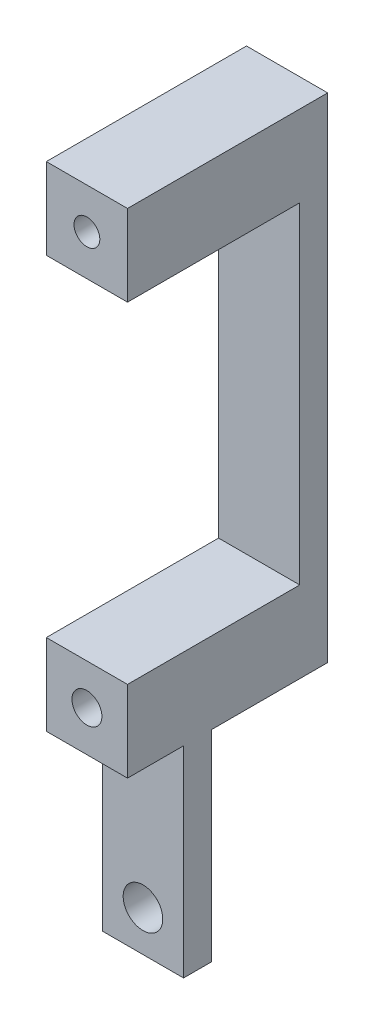
SolidWorks part; units mm, degrees
ref_plane "Front Plane" through (0, 0, 0) normal (0, 0, 1) x (1, 0, 0)
ref_plane "Top Plane" through (0, 0, 0) normal (0, 1, 0) x (1, 0, 0)
ref_plane "Right Plane" through (0, 0, 0) normal (1, 0, 0) x (0, 0, -1)
sketch "Sketch1" plane through (0, 0, 0) normal (0, 0, 1) x (1, 0, 0)
  line L1 (0, 0) -> (13.843, 0)
  line L2 (0, 0) -> (0, 48.133)
  line L3 (0, 48.133) -> (13.843, 48.133)
  line L4 (13.843, 0) -> (13.843, 48.133)
  dimension "D1" = 48.133
  dimension "D2" = 13.843
extrude "Boss-Extrude1" add sketch "Sketch1" along normal blind 4.7625
sketch "Sketch2" plane through (0, 0, 4.7625) normal (0, 0, 1) x (1, 0, 0)
  line L0 (13.843, 0) -> (13.843, 48.133) construction
  line L1 (0, 48.133) -> (13.843, 48.133)
  line L2 (0, 48.133) -> (0, 34.29)
  line L3 (0, 34.29) -> (13.843, 34.29)
  line L4 (13.843, 48.133) -> (13.843, 34.29)
  dimension "D1" = 13.843
extrude "Boss-Extrude2" add sketch "Sketch2" along normal blind 9.5567
sketch "Sketch3" plane through (0, 0, 0) normal (0, 0, -1) x (-1, 0, 0)
  line L0 (0, 0) -> (-13.843, 0) construction
  circle A0 centre (-6.9215, 6.9215) radius 3.3782
  point P2 (0, 0)
  point P5 (-6.9215, 0)
  dimension "D1" = 6.9215
  dimension "D2" = 6.7564
extrude "Cut-Extrude1" cut sketch "Sketch3" against normal blind 9.5567
sketch "Sketch4" plane through (0, 0, 0) normal (0, 0, -1) x (-1, 0, 0)
  line L0 (-13.843, 48.133) -> (0, 48.133) construction
  circle A0 centre (-6.9215, 41.2115) radius 2.5527
  point P1 (0, 0)
  point P5 (-6.9215, 48.133)
  dimension "D2" = 5.1054
  dimension "D1" = 6.9215
extrude "Cut-Extrude2" cut sketch "Sketch4" against normal blind 16.9228
sketch "Sketch5" plane through (0, 0, 0) normal (0, 0, -1) x (-1, 0, 0)
  line L0 (0, 48.133) -> (0, 0) construction
  line L1 (-13.843, 48.133) -> (0, 48.133)
  line L2 (-13.843, 48.133) -> (-13.843, 34.29)
  line L3 (-13.843, 34.29) -> (0, 34.29)
  line L4 (0, 48.133) -> (0, 34.29)
  dimension "D1" = 13.843
extrude "Boss-Extrude3" add sketch "Sketch5" along normal blind 19.812
sketch "Sketch6" plane through (0, 0, -19.812) normal (0, 0, -1) x (-1, 0, 0)
  line L0 (0, 34.29) -> (0, 48.133) construction
  line L1 (-9.7319, 46.0829) -> (-12.5454, 41.2133)
  line L2 (-12.5454, 41.2133) -> (-9.735, 36.342)
  line L3 (-9.735, 36.342) -> (-4.1111, 36.3401)
  line L4 (-4.1111, 36.3401) -> (-1.2976, 41.2097)
  line L5 (-1.2976, 41.2097) -> (-4.108, 46.081)
  line L6 (-4.108, 46.081) -> (-9.7319, 46.0829)
  line L7 (0, 48.133) -> (-13.843, 48.133) construction
  circle A0 centre (-6.9215, 41.2115) radius 4.8704 construction
  point P1 (0, 0)
  point P11 (0, 41.2115)
  point P12 (0, 0)
  point P15 (-6.9215, 48.133)
  dimension "D1" = 9.7409
extrude "Cut-Extrude3" cut sketch "Sketch6" against normal blind 19.812
sketch "Sketch7" plane through (0, 48.133, 0) normal (0, 1, 0) x (1, 0, 0)
  line L0 (13.843, -14.3192) -> (13.843, 19.812) construction
  line L1 (0, 19.812) -> (13.843, 19.812)
  line L2 (0, 19.812) -> (0, 15.0495)
  line L3 (0, 15.0495) -> (13.843, 15.0495)
  line L4 (13.843, 19.812) -> (13.843, 15.0495)
  dimension "D1" = 4.7625
extrude "Boss-Extrude4" add sketch "Sketch7" along normal blind 70.2818
sketch "Sketch8" plane through (0, 0, -15.0495) normal (0, 0, 1) x (1, 0, 0)
  line L0 (0, 118.4148) -> (0, 48.133) construction
  line L1 (0, 118.4148) -> (13.843, 118.4148)
  line L2 (0, 118.4148) -> (0, 104.5718)
  line L3 (0, 104.5718) -> (13.843, 104.5718)
  line L4 (13.843, 118.4148) -> (13.843, 104.5718)
  line L5 (13.843, 118.4148) -> (13.843, 48.133) construction
  line L6 (0, 118.4148) -> (13.843, 118.4148) construction
  dimension "D1" = 13.843
extrude "Boss-Extrude5" add sketch "Sketch8" along normal blind 29.3687
sketch "Sketch9" plane through (0, 0, -19.812) normal (0, 0, -1) x (-1, 0, 0)
  line L0 (-13.843, 118.4148) -> (0, 118.4148) construction
  line L1 (-8.9966, 115.0874) -> (-11.0716, 111.4933)
  line L2 (-11.0716, 111.4933) -> (-8.9966, 107.8992)
  line L3 (-8.9966, 107.8992) -> (-4.8464, 107.8992)
  line L4 (-4.8464, 107.8992) -> (-2.7714, 111.4933)
  line L5 (-2.7714, 111.4933) -> (-4.8464, 115.0874)
  line L6 (-4.8464, 115.0874) -> (-8.9966, 115.0874)
  circle A0 centre (-6.9215, 111.4933) radius 3.5941 construction
  point P1 (0, 0)
  point P11 (-6.9215, 118.4148)
  dimension "D1" = 7.1882
  dimension "D2" = 6.9215
extrude "Cut-Extrude4" cut sketch "Sketch9" against normal blind 7.62
sketch "Sketch10" plane through (0, 0, -12.192) normal (0, 0, -1) x (-1, 0, 0)
  line L0 (-13.843, 118.4148) -> (0, 118.4148) construction
  circle A0 centre (-6.9215, 111.4933) radius 2.2
  point P2 (0, 0)
  point P5 (-6.9215, 118.4148)
  dimension "D2" = 4.4
  dimension "D1" = 6.9215
extrude "Cut-Extrude5" cut sketch "Sketch10" against normal through all
